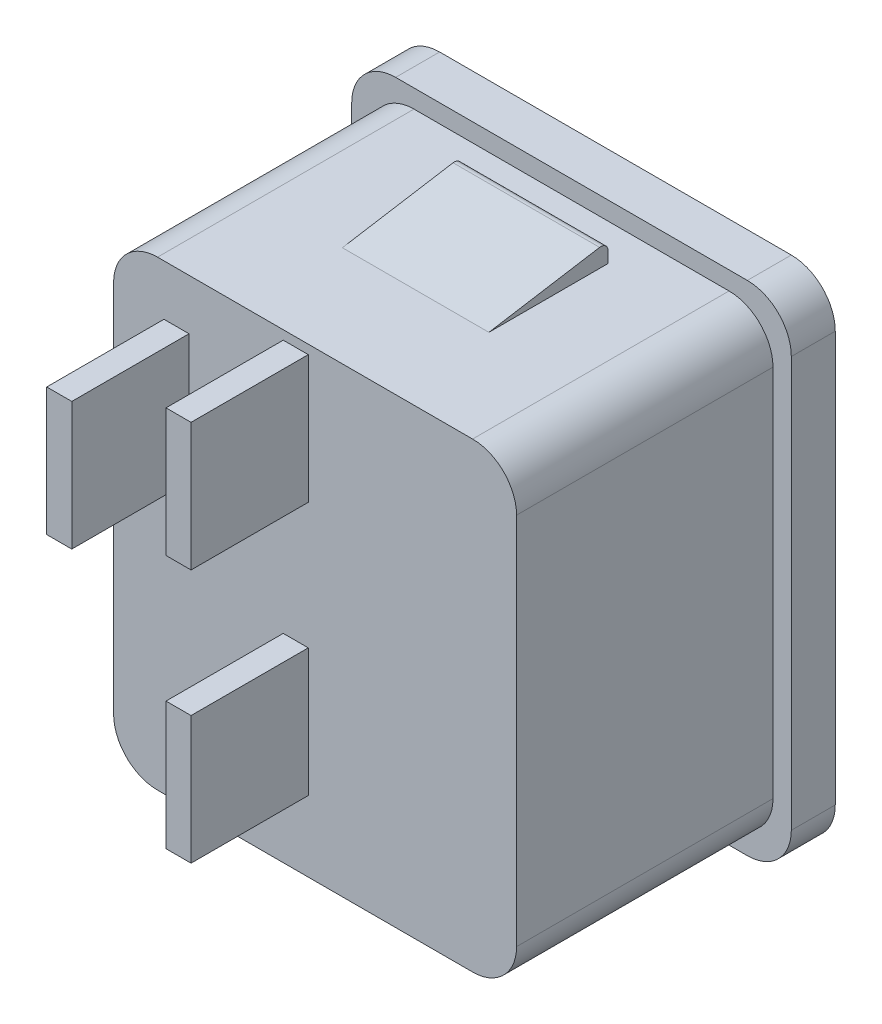
SolidWorks part; units mm, degrees
ref_plane "Front Plane" through (0, 0, 0) normal (0, 0, 1) x (1, 0, 0)
ref_plane "Top Plane" through (0, 0, 0) normal (0, 1, 0) x (1, 0, 0)
ref_plane "Right Plane" through (0, 0, 0) normal (1, 0, 0) x (0, 0, -1)
sketch "Sketch1" plane through (0, 0, 0) normal (0, 0, 1) x (1, 0, 0)
  line L1 (-15, -17) -> (15, -17)
  line L2 (-15, -17) -> (-15, 17)
  line L3 (-15, 17) -> (15, 17)
  line L4 (15, -17) -> (15, 17)
  line L5 (-15, -17) -> (15, 17) construction
  line L6 (-15, 17) -> (15, -17) construction
  point P0 (0, 0)
  dimension "D1" = 30
  dimension "D2" = 34
extrude "Boss-Extrude1" add sketch "Sketch1" against normal blind 3
sketch "Sketch3" plane through (0, 0, 0) normal (0, 0, 1) x (1, 0, 0)
  line L1 (-13.75, -15.75) -> (13.75, -15.75)
  line L2 (-13.75, -15.75) -> (-13.75, 15.75)
  line L3 (-13.75, 15.75) -> (13.75, 15.75)
  line L4 (13.75, -15.75) -> (13.75, 15.75)
  line L5 (-13.75, -15.75) -> (13.75, 15.75) construction
  line L6 (-13.75, 15.75) -> (13.75, -15.75) construction
  point P0 (0, 0)
  dimension "D1" = 31.5
  dimension "D2" = 27.5
extrude "Boss-Extrude2" add sketch "Sketch3" along normal blind 25.5
fillet "Fillet1" radius 3 8 edges at (13.75, 15.75, 12.75) (-13.75, 15.75, 12.75) (-13.75, -15.75, 12.75) (13.75, -15.75, 12.75) (15, -17, -1.5) (-15, -17, -1.5) (15, 17, -1.5) (-15, 17, -1.5)
sketch "Sketch4" plane through (0, 0, 0) normal (1, 0, 0) x (0, 0, -1)
  line L0 (-2.5, 15.75) -> (-2.5, 16.5)
  line L1 (-3.0812, 16.9934) -> (-10.6362, 15.75)
  line L3 (0, 15.75) -> (-25.5, 15.75) construction
  line L4 (0, 17) -> (0, 14) construction
  line L5 (-2.5, 15.75) -> (-10.6362, 15.75)
  line L6 (0, 17) -> (3, 17) construction
  line L7 (0, 0) -> (-16.8329, 0) construction
  line L8 (-2.5, -15.75) -> (-10.6362, -15.75)
  line L9 (-3.0812, -16.9934) -> (-10.6362, -15.75)
  line L10 (-2.5, -15.75) -> (-2.5, -16.5)
  arc A0 (-2.5, 16.5) -> (-3.0812, 16.9934) centre (-3, 16.5) ccw
  arc A1 (-2.5, -16.5) -> (-3.0812, -16.9934) centre (-3, -16.5) cw
  dimension "D2" = 0.5
  dimension "D1" = 2.5
extrude "Boss-Extrude3" add sketch "Sketch4" along normal mid plane 10
sketch "Sketch5" plane through (0, 0, 25.5) normal (0, 0, 1) x (1, 0, 0)
  line L1 (-10.3121, 12.2965) -> (-8.6022, 12.2965)
  line L2 (-10.3121, 12.2965) -> (-10.3121, 3.5697)
  line L3 (-10.3121, 3.5697) -> (-8.6022, 3.5697)
  line L4 (-8.6022, 12.2965) -> (-8.6022, 3.5697)
  line L5 (-10.3121, 12.2965) -> (-8.6022, 3.5697) construction
  line L6 (-10.3121, 3.5697) -> (-8.6022, 12.2965) construction
  line L7 (-2.1731, 15.1315) -> (-0.4631, 15.1315)
  line L8 (-2.1731, 15.1315) -> (-2.1731, 6.4047)
  line L9 (-2.1731, 6.4047) -> (-0.4631, 6.4047)
  line L10 (-0.4631, 15.1315) -> (-0.4631, 6.4047)
  line L11 (-2.1731, 15.1315) -> (-0.4631, 6.4047) construction
  line L12 (-2.1731, 6.4047) -> (-0.4631, 15.1315) construction
  line L13 (-2.1731, -2.1979) -> (-0.4631, -2.1979)
  line L14 (-2.1731, -2.1979) -> (-2.1731, -10.9246)
  line L15 (-2.1731, -10.9246) -> (-0.4631, -10.9246)
  line L16 (-0.4631, -2.1979) -> (-0.4631, -10.9246)
  line L17 (-2.1731, -2.1979) -> (-0.4631, -10.9246) construction
  line L18 (-2.1731, -10.9246) -> (-0.4631, -2.1979) construction
  point P0 (-9.4571, 7.9331)
  point P5 (-1.3181, 10.7681)
  point P11 (-1.3181, -6.5613)
extrude "Cut-Extrude1" cut sketch "Sketch5" against normal blind 8 flip side to cut
